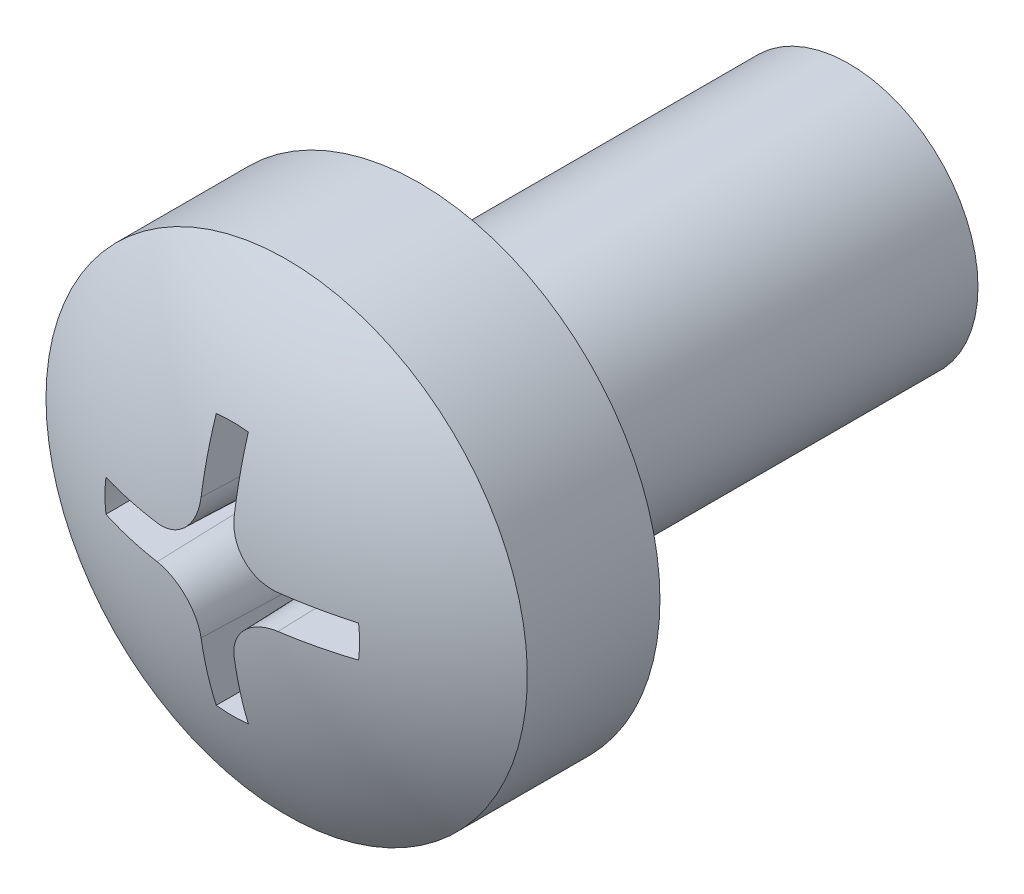
SolidWorks part; units mm, degrees
material "普通碳钢"
ref_plane "Plane1" through (0, 0, 0) normal (0, 0, 1) x (1, 0, 0)
ref_plane "Plane2" through (0, 0, 0) normal (0, 1, 0) x (1, 0, 0)
ref_plane "Plane3" through (0, 0, 0) normal (1, 0, 0) x (0, 0, -1)
sketch "Sketch1" plane through (0, 0, 0) normal (0, 0, 1) x (1, 0, 0)
  circle A0 centre (0, 0) radius 1.5
  dimension "D1" = 3
extrude "Base-Extrude" add sketch "Sketch1" along normal blind 5 and the other way blind 0.0001
sketch "Sketch6" plane through (0, 0, 0) normal (0, 1, 0) x (1, 0, 0)
  line L0 (0, 0.3936) -> (0, -34.4908) construction
  line L1 (0, -5) -> (0, 0.0001) construction
  line L2 (0, -5) -> (2.8, -5)
  line L3 (2.8, -5) -> (2.8, -6.5425)
  line L4 (0, -7.4) -> (0, -5)
  line L5 (-1.5, -5) -> (1.5, -5) construction
  arc A0 (2.8, -6.5425) -> (0, -7.4) centre (0, -2.4) cw
  dimension "D1" = 2.4
  dimension "D9" = 5
  dimension "D8" = 2.8
revolve "Boss-Revolve2" add sketch "Sketch6" angle 360 about L0
ref_plane "Plane6" through (0, 0, 7.7) normal (0, 0, -1) x (-1, 0, 0)
sketch "Sketch7" plane through (0, 0, 7.7) normal (0, 0, -1) x (-1, 0, 0)
  line L0 (-7.1, 0) -> (5.9, 0) construction
  line L1 (0, 7.5) -> (0, -7) construction
  line L2 (0.205, 1.4859) -> (0.205, 0.7082)
  line L3 (0, 0) -> (4.9858, 4.9858) construction
  line L4 (1.4859, 0.205) -> (0.703, 0.2082)
  line L5 (1.4859, -0.205) -> (0.703, -0.2082)
  line L6 (0.205, -1.4859) -> (0.205, -0.7082)
  line L7 (-0.205, -1.4859) -> (-0.205, -0.7082)
  line L8 (-1.4859, -0.205) -> (-0.703, -0.2082)
  line L9 (-1.4859, 0.205) -> (-0.703, 0.2082)
  line L10 (-0.205, 1.4859) -> (-0.205, 0.7082)
  arc A0 (-0.205, 1.4859) -> (0.205, 1.4859) centre (0, 0) cw
  arc A1 (1.4859, -0.205) -> (1.4859, 0.205) centre (0, 0) ccw
  arc A2 (0.205, 0.7082) -> (0.703, 0.2082) centre (0.705, 0.7082) ccw
  arc A3 (-0.205, 0.7082) -> (-0.703, 0.2082) centre (-0.705, 0.7082) cw
  arc A4 (-0.205, -1.4859) -> (0.205, -1.4859) centre (0, 0) ccw
  arc A5 (-0.205, -0.7082) -> (-0.703, -0.2082) centre (-0.705, -0.7082) ccw
  arc A6 (-1.4859, -0.205) -> (-1.4859, 0.205) centre (0, 0) cw
  arc A7 (0.703, -0.2082) -> (0.205, -0.7082) centre (0.705, -0.7082) ccw
  dimension "D1" = 0.5
  dimension "D10" = 1.5
  dimension "D11" = 0.41
extrude "Cut-Extrude1" cut sketch "Sketch7" along normal blind 1.8 draft 2
